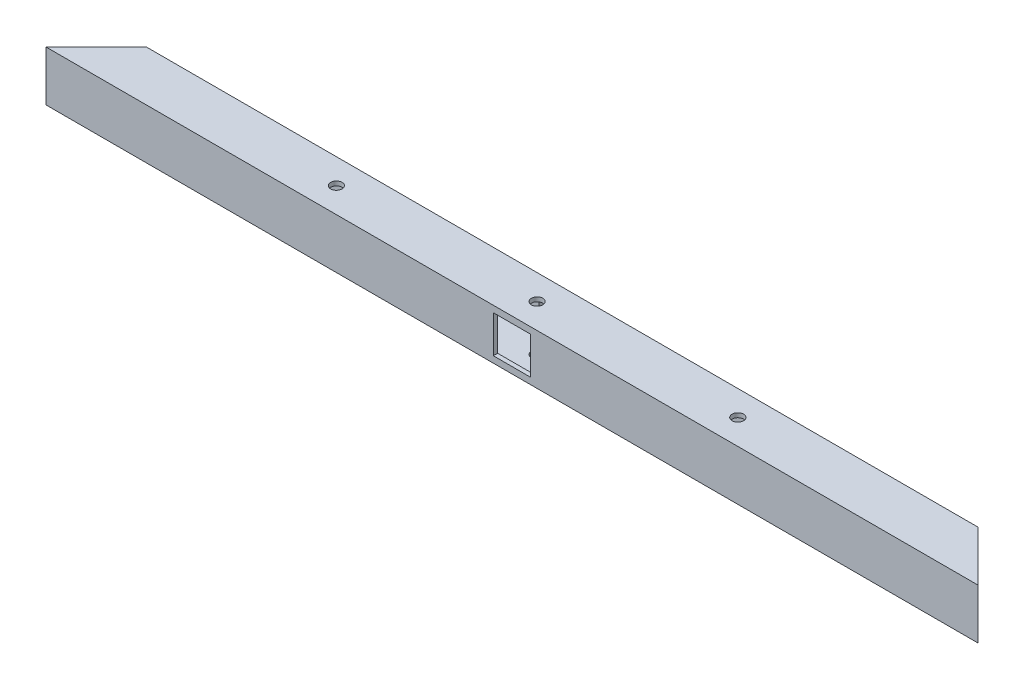
SolidWorks part; units mm, degrees
ref_plane "Front Plane" through (0, 0, 0) normal (0, 0, 1) x (1, 0, 0)
ref_plane "Top Plane" through (0, 0, 0) normal (0, 1, 0) x (1, 0, 0)
ref_plane "Right Plane" through (0, 0, 0) normal (1, 0, 0) x (0, 0, -1)
sketch "Sketch1" plane through (0, 0, 0) normal (0, 1, 0) x (1, 0, 0)
  line L0 (-325, -12.5) -> (-290, 22.5)
  line L1 (-290, 22.5) -> (290, 22.5)
  line L3 (-325, -12.5) -> (325, -12.5)
  line L7 (325, -12.5) -> (290, 22.5)
  dimension "D1" = 650
  dimension "D2" = 45
  dimension "D3" = 45
  dimension "D4" = 35
extrude "Boss-Extrude1" add sketch "Sketch1" along normal blind 35
shell "Shell1" thickness 3
sketch "Sketch2" plane through (0, 0, 12.5) normal (0, 0, 1) x (1, 0, 0)
  line L1 (-13, 30.5) -> (13, 30.5)
  line L2 (-13, 30.5) -> (-13, 4.5)
  line L3 (-13, 4.5) -> (13, 4.5)
  line L4 (13, 30.5) -> (13, 4.5)
  line L5 (-13, 30.5) -> (13, 4.5) construction
  line L6 (-13, 4.5) -> (13, 30.5) construction
  line L8 (-325, 35) -> (325, 35) construction
  point P0 (0, 17.5)
  dimension "D1" = 26
  dimension "D2" = 26
  dimension "D3" = 17.5
extrude "Cut-Extrude1" cut sketch "Sketch2" against normal through all
sketch "Sketch3" plane through (0, 35, 0) normal (0, 1, 0) x (1, 0, 0)
  line L0 (290, 22.5) -> (-290, 22.5) construction
  circle A0 centre (0, 5) radius 4
  circle A1 centre (140, 5) radius 4
  circle A2 centre (-140, 5) radius 4
  dimension "D1" = 8
  dimension "D3" = 8
  dimension "D5" = 8
  dimension "D2" = 17.5
  dimension "D4" = 140
  dimension "D6" = 140
extrude "Cut-Extrude2" cut sketch "Sketch3" against normal through all
